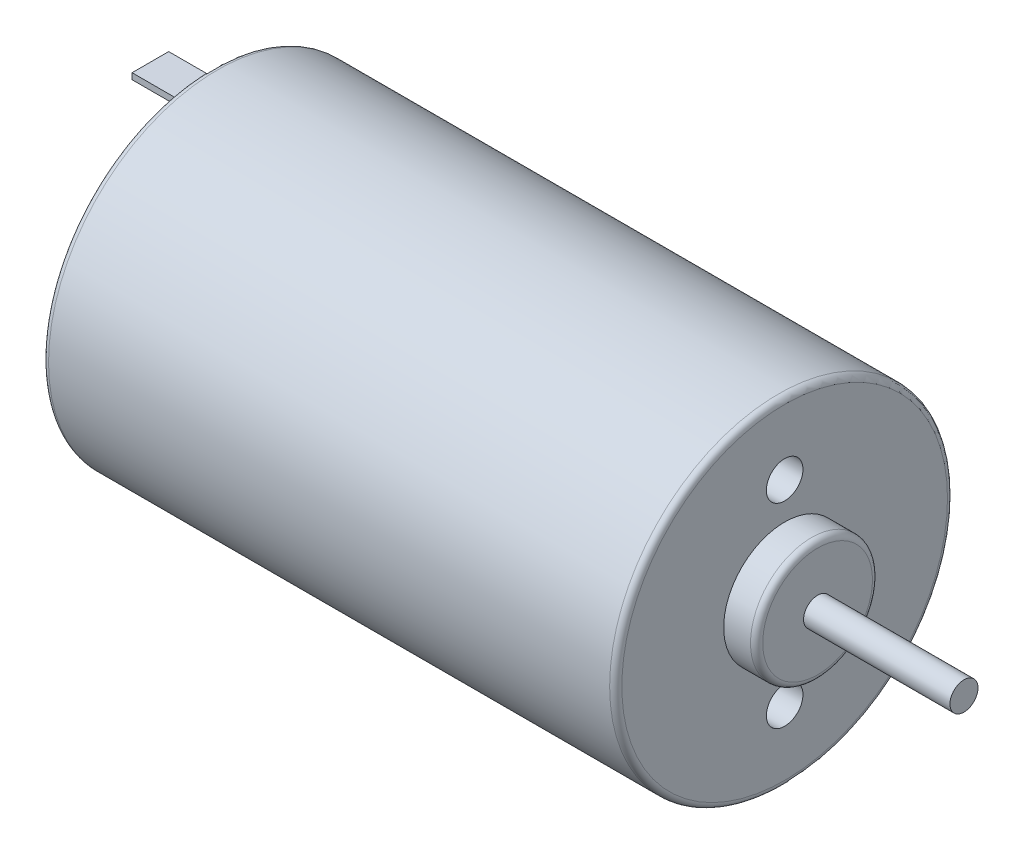
SolidWorks part; units mm, degrees
ref_plane "Front Plane" through (0, 0, 0) normal (0, 0, 1) x (1, 0, 0)
ref_plane "Top Plane" through (0, 0, 0) normal (0, 1, 0) x (1, 0, 0)
ref_plane "Right Plane" through (0, 0, 0) normal (1, 0, 0) x (0, 0, -1)
sketch "Sketch1" plane through (0, 0, 0) normal (1, 0, 0) x (0, 0, -1)
  circle A0 centre (0, 0) radius 13.85
  dimension "D1" = 27.7
extrude "Boss-Extrude1" add sketch "Sketch1" along normal blind 47
sketch "Sketch2" plane through (47, 0, 0) normal (1, 0, 0) x (0, 0, -1)
  circle A0 centre (0, 0) radius 5
  dimension "D1" = 10
extrude "Boss-Extrude2" add sketch "Sketch2" along normal blind 2.7
sketch "Sketch3" plane through (49.7, 0, 0) normal (1, 0, 0) x (0, 0, -1)
  circle A0 centre (0, 0) radius 1.15
  dimension "D1" = 2.3
extrude "Boss-Extrude3" add sketch "Sketch3" along normal blind 12
sketch "Sketch4" plane through (0, 0, 0) normal (-1, 0, 0) x (0, 0, 1)
  circle A0 centre (0, 0) radius 5
  dimension "D1" = 10
extrude "Boss-Extrude4" add sketch "Sketch4" along normal blind 2
sketch "Sketch5" plane through (-2, 0, 0) normal (-1, 0, 0) x (0, 0, 1)
  circle A0 centre (0, 0) radius 1.15
  dimension "D1" = 2.3
extrude "Boss-Extrude5" add sketch "Sketch5" along normal blind 0.75
sketch "Sketch6" plane through (0, 0, 0) normal (-1, 0, 0) x (0, 0, 1)
  line L0 (-13.85, 0) -> (13.85, 0) construction
  line L1 (-1.5, 11.65) -> (1.5, 11.65)
  line L2 (-1.5, 11.65) -> (-1.5, 11.15)
  line L3 (-1.5, 11.15) -> (1.5, 11.15)
  line L4 (1.5, 11.65) -> (1.5, 11.15)
  line L5 (-1.5, 11.65) -> (1.5, 11.15) construction
  line L6 (-1.5, 11.15) -> (1.5, 11.65) construction
  line L7 (-1.5, -11.15) -> (1.5, -11.65) construction
  line L8 (-1.5, -11.65) -> (1.5, -11.15) construction
  line L9 (1.5, -11.65) -> (1.5, -11.15)
  line L10 (-1.5, -11.15) -> (1.5, -11.15)
  line L11 (-1.5, -11.65) -> (-1.5, -11.15)
  line L12 (-1.5, -11.65) -> (1.5, -11.65)
  circle A0 centre (0, 0) radius 13.85 construction
  point P0 (0, 11.4)
  point P15 (0, -11.4)
  dimension "D1" = 11.15
  dimension "D2" = 0.5
  dimension "D3" = 3
extrude "Boss-Extrude6" add sketch "Sketch6" along normal blind 5
sketch "Sketch7" plane through (47, 0, 0) normal (1, 0, 0) x (0, 0, -1)
  line L0 (-13.85, 0) -> (13.85, 0) construction
  circle A0 centre (0, 8) radius 1.5
  circle A1 centre (0, 0) radius 13.85 construction
  circle A2 centre (0, -8) radius 1.5
  dimension "D1" = 8
  dimension "D2" = 3
extrude "Cut-Extrude1" cut sketch "Sketch7" against normal blind 5
fillet "Fillet1" radius 0.5 4 edges at (49.7, 0, -5) (-2, 0, 5) (0, 0, -13.85) (47, 0, -13.85)
